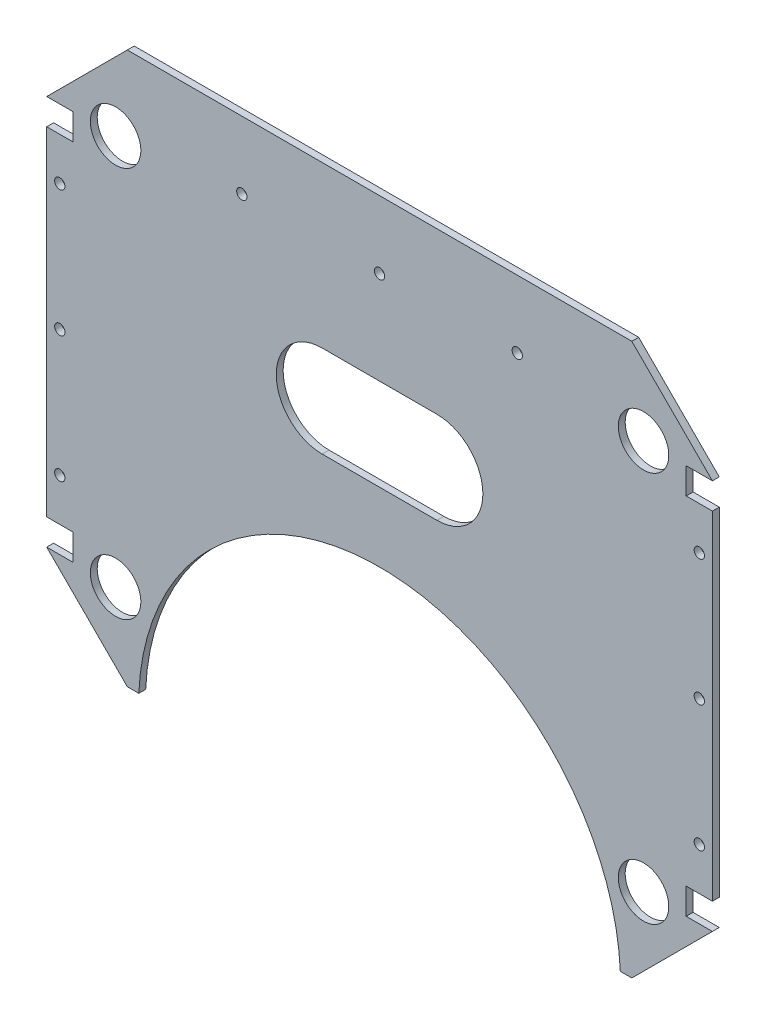
SolidWorks part; units mm, degrees
ref_plane "Plan de face" through (0, 0, 0) normal (0, 0, 1) x (1, 0, 0)
ref_plane "Plan de dessus" through (0, 0, 0) normal (0, 1, 0) x (1, 0, 0)
ref_plane "Plan de droite" through (0, 0, 0) normal (1, 0, 0) x (0, 0, -1)
sketch "Esquisse1" plane through (0, 0, 0) normal (0, 0, 1) x (1, 0, 0)
  line L0 (-145, 85) -> (-109.8862, 120.1138)
  line L1 (-109.8862, 120.1138) -> (-105, 125) construction
  line L2 (109.8862, 120.1138) -> (145, 85)
  line L3 (-85, 145) -> (85, 145) construction
  line L4 (105, -125) -> (109.8862, -120.1138) construction
  line L5 (-145, -145) -> (145, 145) construction
  line L6 (-145, 145) -> (145, -145) construction
  line L7 (85, 145) -> (105, 125) construction
  line L8 (-105, -125) -> (-85, -145) construction
  line L9 (-105, -125) -> (105, -125) construction
  line L10 (-105, 125) -> (105, 125) construction
  line L11 (85, -145) -> (105, -125) construction
  line L12 (-105, 125) -> (-85, 145) construction
  line L13 (105, 125) -> (109.8862, 120.1138) construction
  line L14 (-85, -145) -> (85, -145) construction
  line L15 (-109.8862, -120.1138) -> (-105, -125) construction
  line L16 (-109.8862, 120.1138) -> (109.8862, 120.1138)
  line L18 (-145, 0) -> (145, 0) construction
  line L19 (145, 85) -> (145, -85)
  line L20 (104.8862, -120.1138) -> (109.8862, -120.1138)
  line L21 (-109.8862, -120.1138) -> (-104.8862, -120.1138)
  line L22 (-145, 85) -> (-145, -85)
  line L24 (109.8862, -120.1138) -> (145, -85)
  line L25 (-145, -85) -> (-109.8862, -120.1138)
  line L28 (0, 125) -> (0, -125) construction
  arc A1 (-104.8862, -120.1138) -> (104.8862, -120.1138) centre (0, -125) cw
  point P0 (0, 0)
  point P30 (-145, 0)
  dimension "D1" = 290
  dimension "D2" = 290
  dimension "D6" = 60
  dimension "D7" = 60
extrude "Boss.-Extru.1" add sketch "Esquisse1" along normal blind 3
sketch "Esquisse21" plane through (0, 0, 3) normal (0, 0, 1) x (1, 0, 0)
  line L0 (0, 0) -> (191.7599, 0) construction
  line L1 (-145, 85) -> (-133.6, 85)
  line L2 (-145, 85) -> (-145, 73.6)
  line L3 (-145, 73.6) -> (-133.6, 73.6)
  line L4 (-133.6, 85) -> (-133.6, 73.6)
  line L5 (0, 0) -> (0, 158.3492) construction
  line L6 (145, 85) -> (145, 73.6)
  line L7 (145, 73.6) -> (133.6, 73.6)
  line L8 (133.6, 85) -> (133.6, 73.6)
  line L9 (145, 85) -> (133.6, 85)
  line L10 (-133.6, -85) -> (-133.6, -73.6)
  line L11 (-145, -73.6) -> (-133.6, -73.6)
  line L12 (-145, -85) -> (-145, -73.6)
  line L13 (-145, -85) -> (-133.6, -85)
  line L14 (145, -85) -> (145, -73.6)
  line L15 (145, -85) -> (133.6, -85)
  line L16 (145, -73.6) -> (133.6, -73.6)
  line L17 (133.6, -85) -> (133.6, -73.6)
  point P5 (-139.3, 79.3)
  point P9 (139.3, 79.3)
  point P19 (-139.3, -79.3)
  point P23 (139.3, -79.3)
  dimension "D1" = 11.4
  dimension "D2" = 11.4
  dimension "D3" = 5.7
  dimension "D4" = 5.7
extrude "Enlèv. mat.-Extru.3" cut sketch "Esquisse21" against normal through all
sketch "Esquisse37" plane through (0, 0, 0) normal (0, 0, -1) x (-1, 0, 0)
  line L0 (-139.3, 73.6) -> (-139.3, -73.6) construction
  line L1 (-133.6, 73.6) -> (-145, 73.6) construction
  line L2 (-145, -73.6) -> (-133.6, -73.6) construction
  line L4 (139.3, 73.6) -> (139.3, -73.6) construction
  line L5 (145, 73.6) -> (133.6, 73.6) construction
  line L6 (133.6, -73.6) -> (145, -73.6) construction
  point P6 (-139.3, 0)
  point P7 (-139.3, -55)
  point P8 (-139.3, 55)
  point P15 (139.3, 0)
  point P16 (139.3, 55)
  point P17 (139.3, -55)
  dimension "D1" = 55
  dimension "D2" = 55
  dimension "D3" = 55
  dimension "D4" = 55
hole_wizard "Dégagement M41" positions "Esquisse39" profile "Esquisse38" hole size "M4" standard "ISO" end condition through all
sketch "Esquisse39" plane through (0, 0, 0) normal (0, 0, -1) x (-1, 0, 0)
  point P1 (-139.3, 55)
  point P4 (-139.3, 0)
  point P7 (-139.3, -55)
  point P10 (139.3, 55)
  point P13 (139.3, 0)
  point P16 (139.3, -55)
sketch "Esquisse38" plane through (139.3, 55, 0) normal (1, 0, 0) x (0, 1, 0)
  line L0 (0, 0) -> (0, 3)
  line L1 (0, 3) -> (2.25, 3)
  line L2 (2.25, 3) -> (2.25, 0)
  line L5 (2.25, 0) -> (0, 0)
  line L11 (0, -6.35) -> (0, 107.95) construction
  dimension "Diamètre du perçage jusqu'au prochain" = 4.5
  dimension "Profondeur du perçage jusqu'au prochain" = 3
sketch "Esquisse40" plane through (0, 0, 3) normal (0, 0, 1) x (1, 0, 0)
  line L0 (-139.2862, 90.7138) -> (139.2862, 90.7138) construction
  line L1 (-109.8862, 120.1138) -> (-145, 85) construction
  line L2 (145, 85) -> (109.8862, 120.1138) construction
  line L3 (109.8862, 120.1138) -> (-109.8862, 120.1138) construction
  point P8 (0, 90.7138)
  point P9 (-60, 90.7138)
  point P10 (60, 90.7138)
  dimension "D1" = 29.4
  dimension "D2" = 60
  dimension "D3" = 60
hole_wizard "Dégagement M42" positions "Esquisse42" profile "Esquisse41" hole size "M4" standard "ISO" end condition through all
sketch "Esquisse42" plane through (0, 0, 3) normal (0, 0, 1) x (1, 0, 0)
  line L0 (-139.2862, 90.7138) -> (139.2862, 90.7138) construction
  point P1 (-60, 90.7138)
  point P4 (0, 90.7138)
  point P8 (60, 90.7138)
sketch "Esquisse41" plane through (-60, 90.7138, 3) normal (1, 0, 0) x (0, -1, 0)
  line L0 (0, 0) -> (0, 3)
  line L1 (0, 3) -> (2.25, 3)
  line L2 (2.25, 3) -> (2.25, 0)
  line L5 (2.25, 0) -> (0, 0)
  line L11 (0, -6.35) -> (0, 107.95) construction
  dimension "Diamètre du perçage jusqu'au prochain" = 4.5
  dimension "Profondeur du perçage jusqu'au prochain" = 3
sketch "Esquisse43" plane through (0, 0, 0) normal (0, 0, -1) x (-1, 0, 0)
  line L0 (-109.8862, 120.1138) -> (109.8862, 120.1138) construction
  line L1 (-104.8862, -120.1138) -> (-109.8862, -120.1138) construction
  line L2 (109.8862, -120.1138) -> (104.8862, -120.1138) construction
  point P0 (-115, 85.1138)
  point P1 (-115, -85.1138)
  point P2 (115, 85.1138)
  point P3 (115, -85.1138)
  dimension "D1" = 30
  dimension "D2" = 35
  dimension "D3" = 30
  dimension "D4" = 35
  dimension "D5" = 30
  dimension "D6" = 35
  dimension "D7" = 30
  dimension "D8" = 35
hole_wizard "Dégagement M201" positions "Esquisse45" profile "Esquisse44" hole size "M20" standard "ISO" end condition through all
sketch "Esquisse45" plane through (0, 0, 0) normal (0, 0, -1) x (-1, 0, 0)
  point P1 (-115, 85.1138)
  point P4 (-115, -85.1138)
  point P7 (115, 85.1138)
  point P10 (115, -85.1138)
sketch "Esquisse44" plane through (115, 85.1138, 0) normal (1, 0, 0) x (0, 1, 0)
  line L0 (0, 0) -> (0, 3)
  line L1 (0, 3) -> (11, 3)
  line L2 (11, 3) -> (11, 0)
  line L5 (11, 0) -> (0, 0)
  line L11 (0, -6.35) -> (0, 107.95) construction
  dimension "Diamètre du perçage jusqu'au prochain" = 22
  dimension "Profondeur du perçage jusqu'au prochain" = 3
sketch "Esquisse46" plane through (0, 0, 0) normal (0, 0, -1) x (-1, 0, 0)
  line L0 (-25, 30.1138) -> (25, 30.1138) construction
  line L1 (-25, 50.1138) -> (25, 50.1138)
  line L2 (-25, 10.1138) -> (25, 10.1138)
  line L3 (-109.8862, 120.1138) -> (109.8862, 120.1138) construction
  line L4 (-145, -73.6) -> (-145, 73.6) construction
  arc A0 (-25, 50.1138) -> (-25, 10.1138) centre (-25, 30.1138) ccw
  arc A1 (25, 10.1138) -> (25, 50.1138) centre (25, 30.1138) ccw
  point P2 (0, 30.1138)
  dimension "D4" = 20
  dimension "D1" = 90
  dimension "D2" = 145
  dimension "D3" = 50
extrude "Enlèv. mat.-Extru.4" cut sketch "Esquisse46" against normal through all
